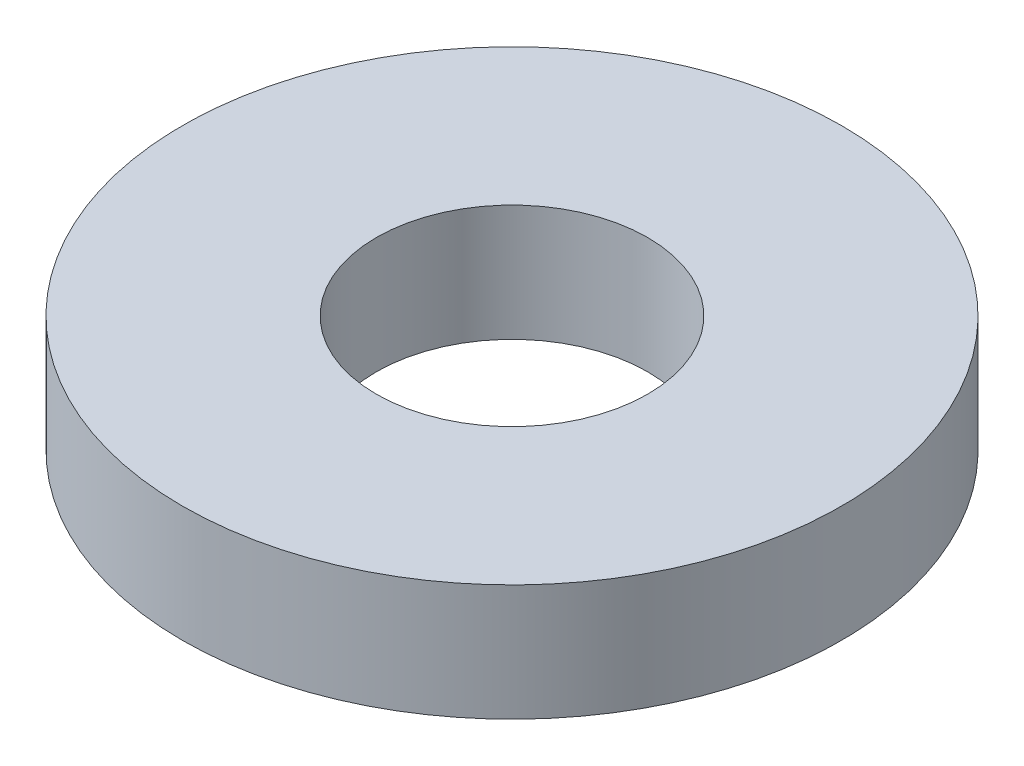
SolidWorks part; units mm, degrees
ref_plane "Plano frontal" through (0, 0, 0) normal (0, 0, 1) x (1, 0, 0)
ref_plane "Plano superior" through (0, 0, 0) normal (0, 1, 0) x (1, 0, 0)
ref_plane "Plano direito" through (0, 0, 0) normal (1, 0, 0) x (0, 0, -1)
sketch "Esboço1" plane through (0, 0, 0) normal (0, 1, 0) x (1, 0, 0)
  circle A0 centre (0, 0) radius 1.75
  circle A1 centre (0, 0) radius 4.25
  dimension "D1" = 3.5
  dimension "D2" = 8.5
extrude "Ressalto-extrusão1" add sketch "Esboço1" along normal blind 1.5
